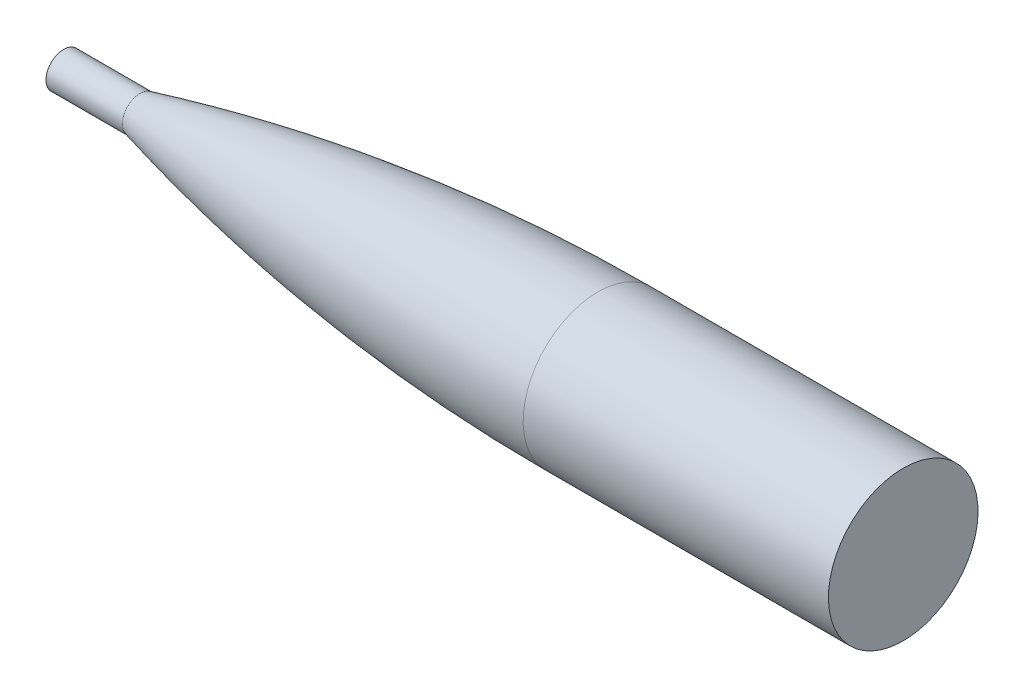
SolidWorks part; units mm, degrees
ref_plane "Front Plane" through (0, 0, 0) normal (0, 0, 1) x (1, 0, 0)
ref_plane "Top Plane" through (0, 0, 0) normal (0, 1, 0) x (1, 0, 0)
ref_plane "Right Plane" through (0, 0, 0) normal (1, 0, 0) x (0, 0, -1)
sketch "Sketch1" plane through (0, 0, 0) normal (0, 0, 1) x (1, 0, 0)
  line L0 (304.8, 49.784) -> (304.8, 0)
  line L1 (304.8, 0) -> (0, 0)
  line L2 (0, 0) -> (0, 11.7484)
  spline S0 degree 4 poles (-29.5658, 3.8633) (-28.9441, 4.0374) (-27.7007, 4.3845) (-25.2159, 5.0746) (-22.1117, 5.9273) (-19.0277, 6.7655) (-15.9353, 7.5966) (-13.5064, 8.2445) (-11.0138, 8.9031) (-8.6496, 9.5239) (-6.017, 10.2074) (-3.9348, 10.7459) (-0.8664, 11.529) (0.5497, 11.8883) (3.0854, 12.5273) (5.1062, 13.0323) (7.1101, 13.5293) (9.1599, 14.0344) (11.1954, 14.5321) (13.2334, 15.0269) (15.805, 15.6465) (18.9103, 16.3873) (22.5507, 17.2447) (26.7272, 18.2131) (31.9522, 19.4057) (42.4129, 21.7425) (62.3339, 25.9764) (110.7705, 35.2251) (160.7073, 42.1599) (207.7023, 46.435) (245.168, 48.3682) (253.7348, 48.741) (260.1614, 48.9835) (264.4463, 49.1304) (268.7317, 49.2625) (273.0175, 49.3798) (277.3037, 49.4823) (281.5902, 49.5699) (285.3296, 49.6334) (288.5217, 49.6785) (291.1667, 49.7098) (293.2638, 49.7311) (295.3592, 49.7488) (297.4702, 49.763) (299.5351, 49.7737) (301.6172, 49.7807) (304.2305, 49.7845) (305.6886, 49.7842) (308.8437, 49.7793) (310.9886, 49.769) (313.6963, 49.7536) (316.1321, 49.733) (318.7003, 49.7073) (321.2035, 49.6765) (323.7502, 49.6404) (326.2925, 49.5988) (328.8544, 49.5518) (331.4237, 49.4993) (333.3523, 49.4559) (334.6374, 49.4252) (335.2799, 49.4094) knots 0 0 0 0 0 0.006994 0.013988 0.027976 0.034844 0.041712 0.048579 0.055447 0.062315 0.069182 0.07605 0.082918 0.088602 0.094285 0.099969 0.105653 0.111336 0.11702 0.122704 0.128387 0.140005 0.151623 0.163241 0.174859 0.198094 0.267801 0.38398 0.709279 0.744133 0.778986 0.790604 0.802222 0.81384 0.825458 0.837075 0.848693 0.860311 0.871929 0.877613 0.883296 0.88898 0.894664 0.900347 0.906031 0.911715 0.917398 0.92424 0.931081 0.937923 0.944764 0.951606 0.958447 0.965289 0.97213 0.979098 0.986065 0.993033 1 1 1 1 1 construction
  spline S1 degree 4 poles (0, 11.7484) (0.4242, 11.8559) (1.2778, 12.0717) (3.0854, 12.5273) (5.1062, 13.0323) (7.1101, 13.5293) (9.1599, 14.0344) (11.1954, 14.5321) (13.2334, 15.0269) (15.805, 15.6465) (18.9103, 16.3873) (22.5507, 17.2447) (26.7272, 18.2131) (31.9522, 19.4057) (42.4129, 21.7425) (62.3339, 25.9764) (110.7705, 35.2251) (160.7073, 42.1599) (207.7023, 46.435) (245.168, 48.3682) (253.7348, 48.741) (260.1614, 48.9835) (264.4463, 49.1304) (268.7317, 49.2625) (273.0175, 49.3798) (277.3037, 49.4823) (281.5902, 49.5699) (285.3296, 49.6334) (288.5217, 49.6785) (291.1667, 49.7098) (293.2638, 49.7311) (295.3592, 49.7488) (297.4702, 49.763) (299.5351, 49.7737) (301.6172, 49.7807) (303.4822, 49.7834) (304.3624, 49.784) (304.8, 49.784) knots 0.082918 0.082918 0.082918 0.082918 0.082918 0.088602 0.094285 0.099969 0.105653 0.111336 0.11702 0.122704 0.128387 0.140005 0.151623 0.163241 0.174859 0.198094 0.267801 0.38398 0.709279 0.744133 0.778986 0.790604 0.802222 0.81384 0.825458 0.837075 0.848693 0.860311 0.871929 0.877613 0.883296 0.88898 0.894664 0.900347 0.906031 0.911715 0.917398 0.917398 0.917398 0.917398 0.917398
  dimension "D1" = 49.784
  dimension "D2" = 304.8
revolve "Revolve1" add sketch "Sketch1" angle 360 about L1
sketch "Sketch2" plane through (304.8, 0, 0) normal (1, 0, 0) x (0, 0, -1)
  circle A0 centre (0, 0) radius 49.784
extrude "Boss-Extrude1" add sketch "Sketch2" along normal blind 203.2
sketch "Sketch3" plane through (0, 0, 0) normal (-1, 0, 0) x (0, 0, 1)
  circle A0 centre (0, 0) radius 11.7484
extrude "Boss-Extrude2" add sketch "Sketch3" along normal blind 50.8
